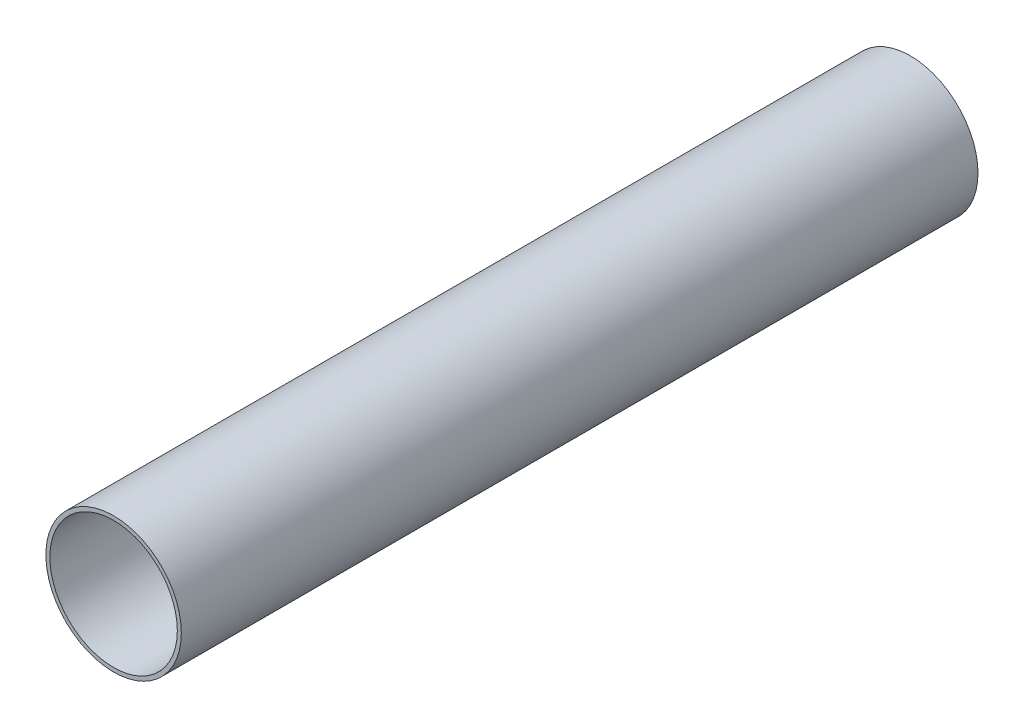
SolidWorks part; units mm, degrees
ref_plane "Front Plane" through (0, 0, 0) normal (0, 0, 1) x (1, 0, 0)
ref_plane "Top Plane" through (0, 0, 0) normal (0, 1, 0) x (1, 0, 0)
ref_plane "Right Plane" through (0, 0, 0) normal (1, 0, 0) x (0, 0, -1)
sketch "Sketch2" plane through (0, 0, 0) normal (0, 0, 1) x (1, 0, 0)
  circle A0 centre (0, 0) radius 17
  circle A1 centre (0, 0) radius 16
  dimension "D1" = 34
  dimension "D2" = 32
extrude "Boss-Extrude2" add sketch "Sketch2" along normal blind 200
